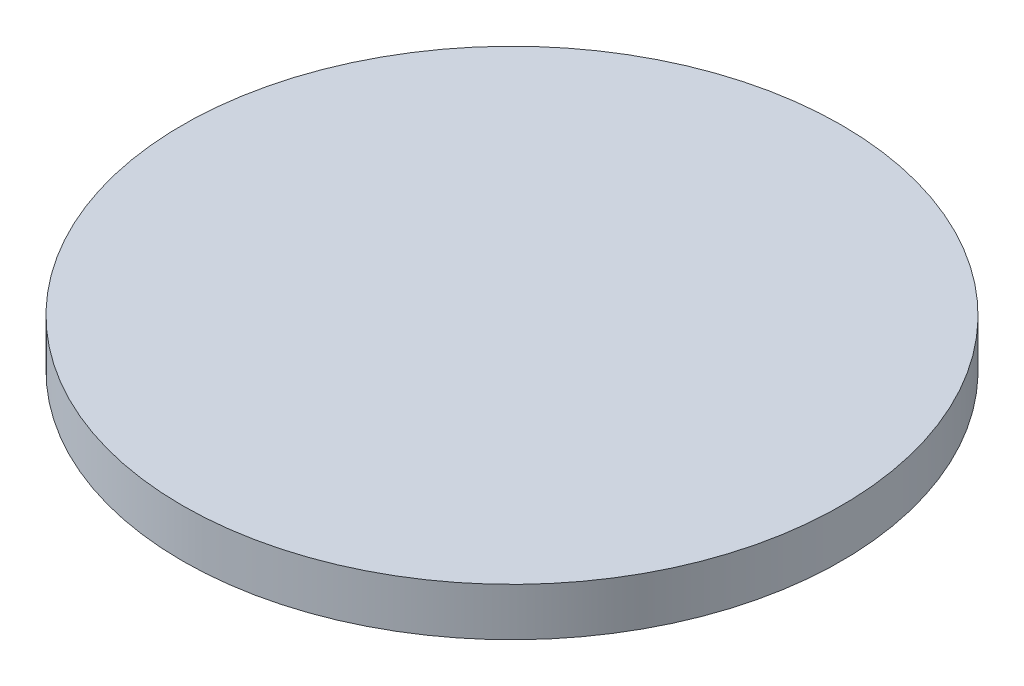
SolidWorks part; units mm, degrees
ref_plane "Front Plane" through (0, 0, 0) normal (0, 0, 1) x (1, 0, 0)
ref_plane "Top Plane" through (0, 0, 0) normal (0, 1, 0) x (1, 0, 0)
ref_plane "Right Plane" through (0, 0, 0) normal (1, 0, 0) x (0, 0, -1)
sketch "Sketch1" plane through (0, 21.8783, 0) normal (0, 1, 0) x (1, 0, 0)
  circle A0 centre (91.8165, -48.1631) radius 17.45
extrude "Boss-Extrude1" add sketch "Sketch1" along normal blind 2.54
